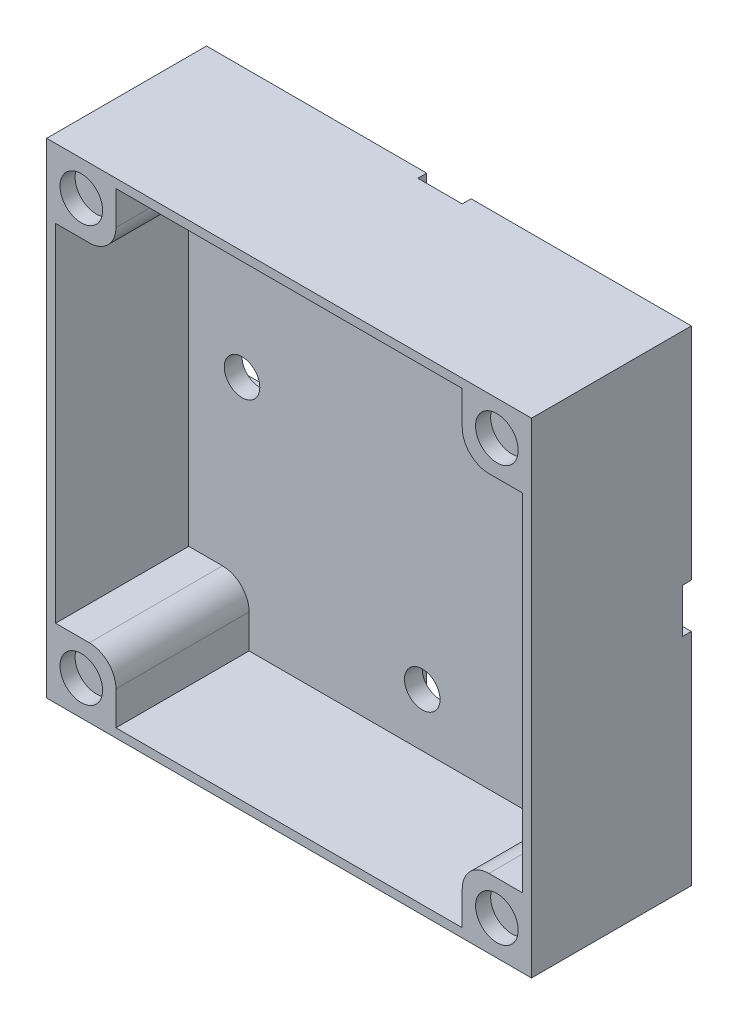
SolidWorks part; units mm, degrees
ref_plane "Přední rovina" through (0, 0, 0) normal (0, 0, 1) x (1, 0, 0)
ref_plane "Horní rovina" through (0, 0, 0) normal (0, 1, 0) x (1, 0, 0)
ref_plane "Pravá rovina" through (0, 0, 0) normal (1, 0, 0) x (0, 0, -1)
sketch "Skica1" plane through (0, 0, 0) normal (0, 0, 1) x (1, 0, 0)
  line L1 (27.3, 27.3) -> (-27.3, 27.3)
  line L2 (27.3, 27.3) -> (27.3, -27.3)
  line L3 (27.3, -27.3) -> (-27.3, -27.3)
  line L4 (-27.3, 27.3) -> (-27.3, -27.3)
  line L5 (27.3, 27.3) -> (-27.3, -27.3) construction
  line L6 (27.3, -27.3) -> (-27.3, 27.3) construction
  point P0 (0, 0)
  point P5 (-27.5, 0)
  point P11 (4.5, 0)
  dimension "D1" = 54.6
  dimension "D2" = 54.6
extrude "Přidat vysunutím2" add sketch "Skica1" along normal blind 3 contours L2 L1 L4 L3
sketch "Skica5" plane through (0, 0, 0) normal (0, 0, -1) x (-1, 0, 0)
  line L0 (-27.3, 27.3) -> (27.3, 27.3) construction
  line L5 (2.5, 27.3) -> (-2.5, 27.3)
  line L10 (27.3, 27.3) -> (27.3, -27.3) construction
  line L11 (-27.3, 2.5) -> (27.3, 2.5)
  line L12 (-27.3, 2.5) -> (-27.3, -2.5)
  line L13 (-27.3, -2.5) -> (27.3, -2.5)
  line L14 (27.3, 2.5) -> (27.3, -2.5)
  line L15 (-27.3, 2.5) -> (27.3, -2.5) construction
  line L16 (-27.3, -2.5) -> (27.3, 2.5) construction
  line L17 (2.5, 27.3) -> (2.5, 2.5)
  line L18 (2.5, 2.5) -> (-2.5, 2.5)
  line L19 (-2.5, 27.3) -> (-2.5, 2.5)
  line L20 (-27.3, 27.3) -> (-27.3, -27.3) construction
  line L21 (-27.3, -27.3) -> (27.3, -27.3) construction
  line L22 (-2.5, -2.5) -> (2.5, -2.5)
  line L23 (-2.5, -2.5) -> (-2.5, -27.3)
  line L24 (-2.5, -27.3) -> (2.5, -27.3)
  line L25 (2.5, -2.5) -> (2.5, -27.3)
  point P0 (0, 0)
  dimension "D1" = 5
  dimension "D2" = 24.8
  dimension "D3" = 5
  dimension "D4" = 24.8
extrude "Odebrat vysunutím3" cut sketch "Skica5" against normal blind 1 contours L11 L14 L13 L12 | L17 L5 L19 L18 | L23 L22 L25 L24
sketch "Skica14" plane through (0, 0, 3) normal (0, 0, 1) x (1, 0, 0)
  line L1 (-27.3, 27.3) -> (27.3, 27.3)
  line L2 (-27.3, 27.3) -> (-27.3, -27.3)
  line L3 (-27.3, -27.3) -> (27.3, -27.3)
  line L4 (27.3, 27.3) -> (27.3, -27.3)
  line L5 (-26.3, 26.3) -> (26.3, 26.3)
  line L6 (-26.3, 26.3) -> (-26.3, -27.3)
  line L7 (-26.3, -27.3) -> (26.3, -27.3)
  line L8 (26.3, 26.3) -> (26.3, -27.3)
  line L9 (-26.3, -27.3) -> (26.3, -27.3)
  line L10 (-26.3, -27.3) -> (-26.3, -26.3)
  line L11 (-26.3, -26.3) -> (26.3, -26.3)
  line L12 (26.3, -27.3) -> (26.3, -26.3)
  line M13 (-27.3, -27.3) -> (27.3, -27.3)
  line M14 (27.3, -27.3) -> (27.3, 27.3)
  line M15 (27.3, 27.3) -> (-27.3, 27.3)
  line M16 (-27.3, 27.3) -> (-27.3, -27.3)
  dimension "D1" = 1
  dimension "D2" = 1
  dimension "D3" = 1
  dimension "D4" = 0
  dimension "D5" = 1
  dimension "D6" = 52.6
extrude "Přidat vysunutím9" add sketch "Skica14" along normal blind 15 contours L5 L8 L6 M13 M14 M15 M16 | L10 L9 L12 L11
sketch "Skica17" plane through (0, 0, 1) normal (0, 0, -1) x (-1, 0, 0)
  line L0 (-27.3, 2.5) -> (-27.3, -2.5) construction
  line L1 (-2.5, -27.3) -> (2.5, -27.3) construction
  line L2 (27.3, 2.5) -> (27.3, -2.5) construction
  line L4 (2.5, 27.3) -> (-2.5, 27.3) construction
  circle A0 centre (-20.3, 0) radius 2
  circle A1 centre (20.3, 0) radius 2
  circle A2 centre (0, 20.3) radius 2
  circle A3 centre (0, -20.3) radius 2
  dimension "D1" = 4
  dimension "D2" = 4
  dimension "D6" = 7
  dimension "D4" = 4
  dimension "D7" = 4
  dimension "D8" = 7
  dimension "D3" = 7
  dimension "D5" = 7
extrude "Odebrat vysunutím8" cut sketch "Skica17" against normal blind 7 contours A2 | A1 | A0 | A3
sketch "Skica19" plane through (0, 0, 0) normal (0, 0, -1) x (-1, 0, 0)
  line L1 (-27.3, 27.3) -> (-19.5, 27.3)
  line L2 (-27.3, 27.3) -> (-27.3, 19.5)
  line L3 (-27.3, 19.5) -> (-19.5, 19.5)
  line L4 (-19.5, 27.3) -> (-19.5, 19.5)
  line L5 (27.3, 27.3) -> (19.5, 27.3)
  line L6 (27.3, 27.3) -> (27.3, 19.5)
  line L7 (27.3, 19.5) -> (19.5, 19.5)
  line L8 (19.5, 27.3) -> (19.5, 19.5)
  line L9 (-27.3, -27.3) -> (-19.5, -27.3)
  line L10 (-27.3, -27.3) -> (-27.3, -19.5)
  line L11 (-27.3, -19.5) -> (-19.5, -19.5)
  line L12 (-19.5, -27.3) -> (-19.5, -19.5)
  line L13 (27.3, -27.3) -> (19.5, -27.3)
  line L14 (27.3, -27.3) -> (27.3, -19.5)
  line L15 (27.3, -19.5) -> (19.5, -19.5)
  line L16 (19.5, -27.3) -> (19.5, -19.5)
  dimension "D1" = 7.8
  dimension "D2" = 7.8
  dimension "D3" = 7.8
  dimension "D4" = 7.8
extrude "Přidat vysunutím10" add sketch "Skica19" against normal blind 18
sketch "Skica20" plane through (0, 0, 18) normal (0, 0, 1) x (1, 0, 0)
  line L0 (-27.3, -27.3) -> (27.3, -27.3) construction
  line L1 (-19.5, -26.3) -> (-19.5, -19.5) construction
  line L2 (-27.3, 27.3) -> (-27.3, -27.3) construction
  line L3 (27.3, 27.3) -> (-27.3, 27.3) construction
  line L4 (27.3, -27.3) -> (27.3, 27.3) construction
  line L5 (-27.3, -27.3) -> (27.3, -27.3) construction
  circle A0 centre (-23.4, -23.4) radius 2.4
  circle A1 centre (-23.4, 23.4) radius 2.4
  circle A2 centre (23.4003, 23.4) radius 2.4
  circle A3 centre (23.4003, -23.4) radius 2.4
  dimension "D1" = 4.8
  dimension "D4" = 4.8
  dimension "D5" = 3.9
  dimension "D7" = 4.8
  dimension "D10" = 4.8
  dimension "D2" = 3.9
  dimension "D3" = 3.9
  dimension "D6" = 3.9
  dimension "D8" = 3.8997
  dimension "D9" = 3.9
  dimension "D11" = 3.9
  dimension "D12" = 3.8997
extrude "Odebrat vysunutím9" cut sketch "Skica20" against normal blind 1.7
fillet "Zaoblit1" radius 3 4 edges at (19.5, 19.5, 10.5) (19.5, -19.5, 10.5) (-19.5, -19.5, 10.5) (-19.5, 19.5, 10.5)
